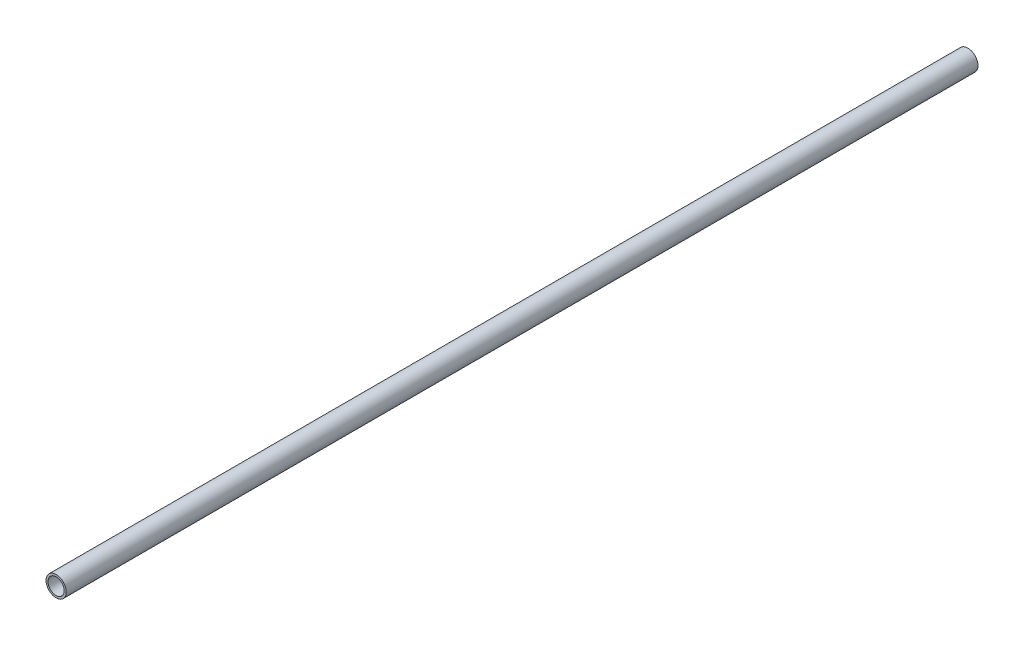
SolidWorks part; units mm, degrees
ref_plane "Front Plane" through (0, 0, 0) normal (0, 0, 1) x (1, 0, 0)
ref_plane "Top Plane" through (0, 0, 0) normal (0, 1, 0) x (1, 0, 0)
ref_plane "Right Plane" through (0, 0, 0) normal (1, 0, 0) x (0, 0, -1)
sketch "Sketch1" plane through (0, 0, 0) normal (0, 0, 1) x (1, 0, 0)
  circle A0 centre (0, 0) radius 5
  circle A1 centre (0, 0) radius 4
  dimension "D1" = 10
  dimension "D2" = 8
extrude "Boss-Extrude1" add sketch "Sketch1" along normal blind 450
